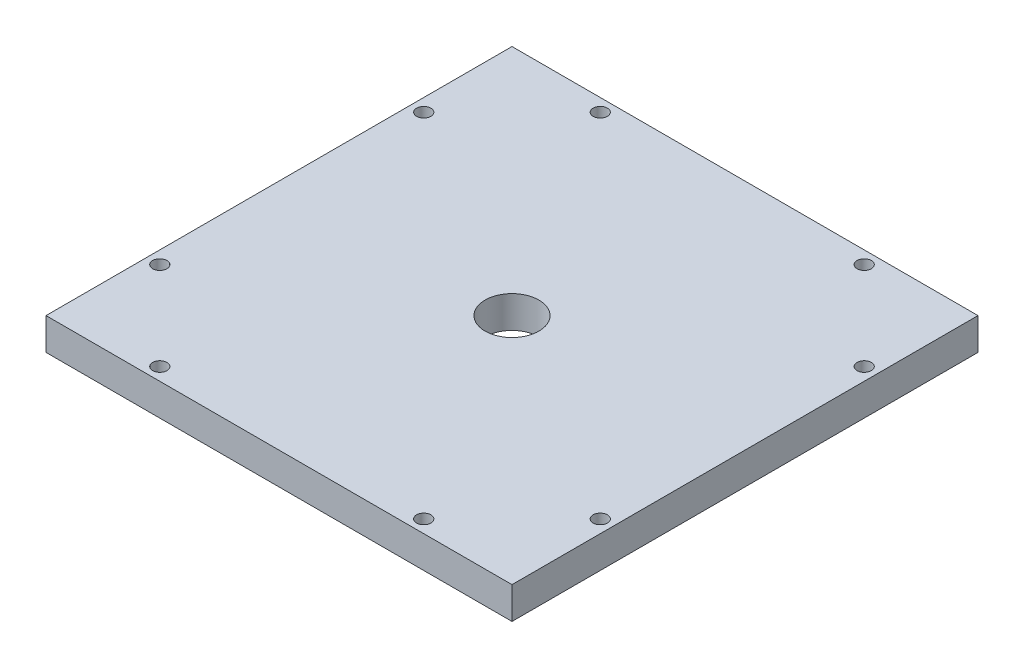
SolidWorks part; units mm, degrees
ref_plane "Front Plane" through (0, 0, 0) normal (0, 0, 1) x (1, 0, 0)
ref_plane "Top Plane" through (0, 0, 0) normal (0, 1, 0) x (1, 0, 0)
ref_plane "Right Plane" through (0, 0, 0) normal (1, 0, 0) x (0, 0, -1)
sketch "Sketch1" plane through (0, 0, 0) normal (0, 1, 0) x (1, 0, 0)
  line L0 (46.355, 92.71) -> (46.355, 0) construction
  line L1 (0, 0) -> (92.71, 0)
  line L2 (0, 0) -> (0, 92.71)
  line L3 (0, 92.71) -> (92.71, 92.71)
  line L4 (92.71, 0) -> (92.71, 92.71)
  line L5 (0, 46.355) -> (92.71, 46.355) construction
  circle A0 centre (46.355, 46.355) radius 5.3578
  dimension "D1" = 92.71
  dimension "D2" = 92.71
extrude "Boss-Extrude1" add sketch "Sketch1" along normal blind 6.35
sketch "Sketch2" plane through (0, 0, 0) normal (0, -1, 0) x (1, 0, 0)
  line L0 (0, 0) -> (92.71, -92.71) construction
  line L1 (46.355, 0) -> (46.355, -92.71) construction
  line L2 (0, 0) -> (92.71, 0) construction
  line L3 (92.71, -92.71) -> (0, -92.71) construction
  line L4 (92.71, -46.355) -> (0, -46.355) construction
  line L5 (92.71, 0) -> (92.71, -92.71) construction
  line L6 (0, -92.71) -> (0, 0) construction
  circle A0 centre (20.1, -2.54) radius 1.4224
  circle A1 centre (2.54, -20.1) radius 1.4224
  circle A2 centre (2.54, -72.61) radius 1.4224
  circle A3 centre (20.1, -90.17) radius 1.4224
  circle A4 centre (72.61, -90.17) radius 1.4224
  circle A5 centre (90.17, -72.61) radius 1.4224
  circle A6 centre (90.17, -20.1) radius 1.4224
  circle A7 centre (72.61, -2.54) radius 1.4224
extrude "Cut-Extrude1" cut sketch "Sketch2" against normal blind 6.35
